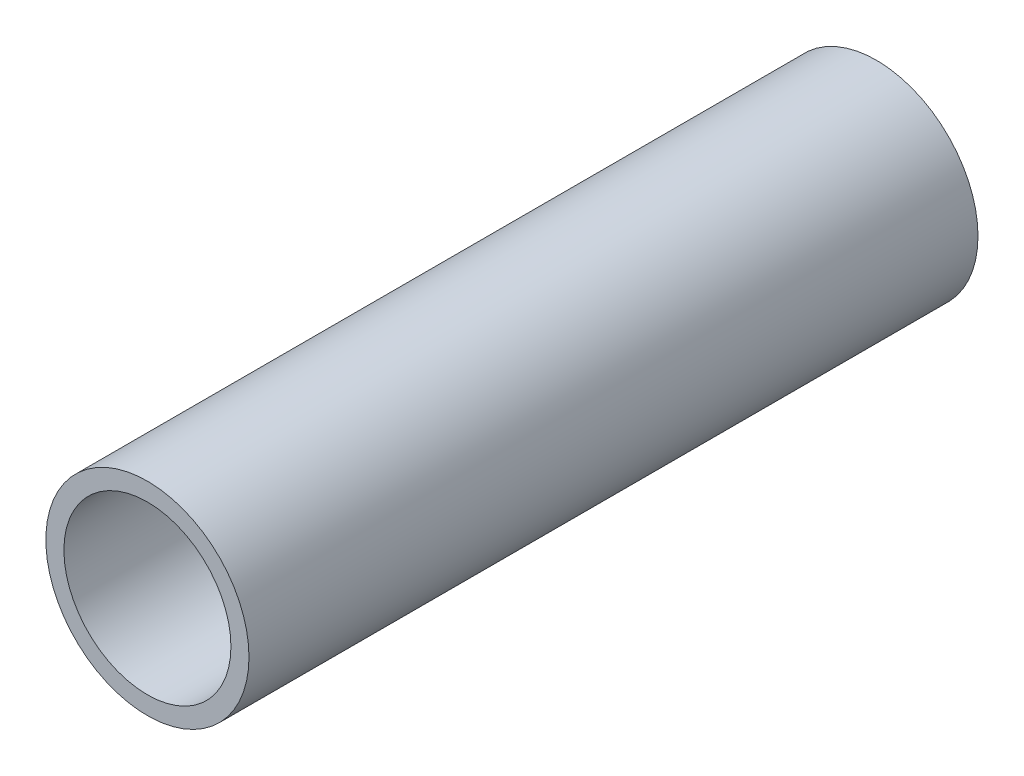
SolidWorks part; units mm, degrees
material "PVC Rigid"
ref_plane "Front Plane" through (0, 0, 0) normal (0, 0, 1) x (1, 0, 0)
ref_plane "Top Plane" through (0, 0, 0) normal (0, 1, 0) x (1, 0, 0)
ref_plane "Right Plane" through (0, 0, 0) normal (1, 0, 0) x (0, 0, -1)
sketch "Sketch1" plane through (0, 0, 0) normal (0, 0, 1) x (1, 0, 0)
  circle A1 centre (0, 0) radius 84.9312
  circle A2 centre (0, 0) radius 69.8436
  dimension "D1" = 15.0876
extrude "Boss-Extrude1" add sketch "Sketch1" along normal blind 609.6
